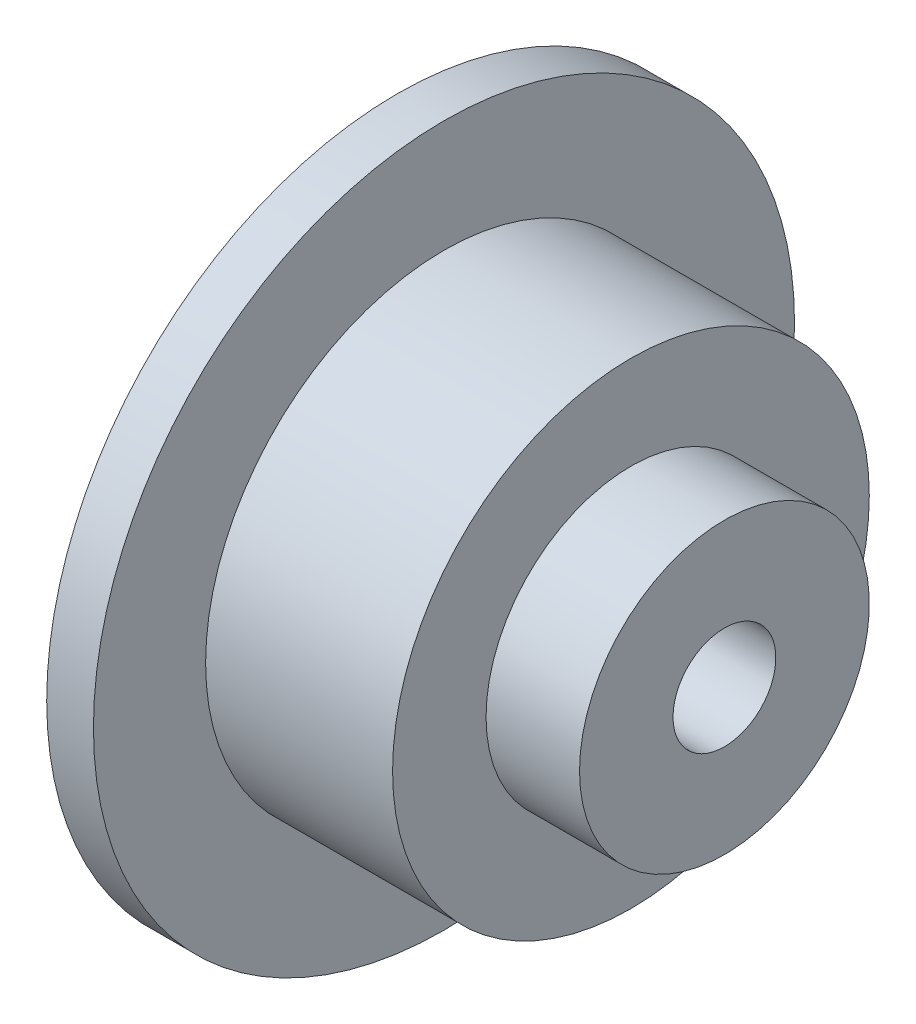
SolidWorks part; units mm, degrees
ref_plane "Front Plane" through (0, 0, 0) normal (0, 0, 1) x (1, 0, 0)
ref_plane "Top Plane" through (0, 0, 0) normal (0, 1, 0) x (1, 0, 0)
ref_plane "Right Plane" through (0, 0, 0) normal (1, 0, 0) x (0, 0, -1)
sketch "Sketch1" plane through (0, 0, 0) normal (0, 1, 0) x (1, 0, 0)
  line L0 (0, 0) -> (25.6413, 0) construction
  line L1 (0, 2.5) -> (0, 7.5)
  line L2 (0, 7.5) -> (1, 7.5)
  line L3 (1, 7.5) -> (1, 5.1)
  line L4 (1, 5.1) -> (5, 5.1)
  line L5 (5, 5.1) -> (5, 3.1)
  line L7 (4, 1.1) -> (4, 2.5)
  line L8 (4, 2.5) -> (0, 2.5)
  line L9 (4, 1.1) -> (7, 1.1)
  line L12 (5, 3.1) -> (7, 3.1)
  line L13 (7, 1.1) -> (7, 3.1)
  dimension "D1" = 5
  dimension "D2" = 7
  dimension "D3" = 6.2
  dimension "D4" = 4
  dimension "D5" = 1
  dimension "D6" = 15
  dimension "D7" = 10.2
  dimension "D8" = 4
  dimension "D9" = 2.2
revolve "Revolve1" add sketch "Sketch1" angle 360 about L0
